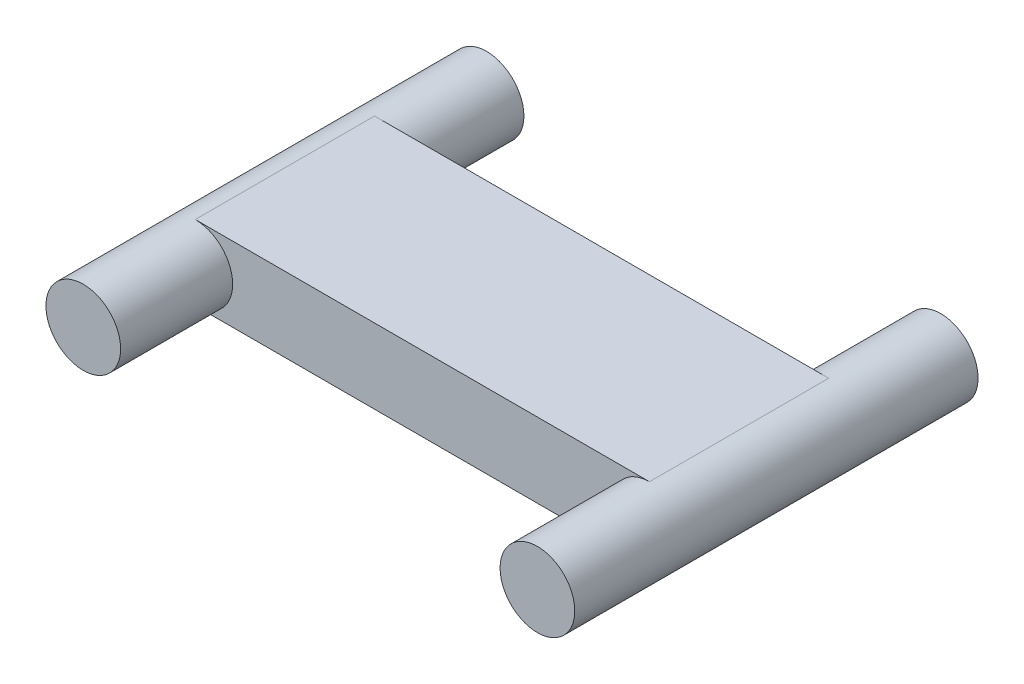
SolidWorks part; units mm, degrees
ref_plane "Front Plane" through (0, 0, 0) normal (0, 0, 1) x (1, 0, 0)
ref_plane "Top Plane" through (0, 0, 0) normal (0, 1, 0) x (1, 0, 0)
ref_plane "Right Plane" through (0, 0, 0) normal (1, 0, 0) x (0, 0, -1)
sketch "Sketch1" plane through (0, 0, 0) normal (0, 0, 1) x (1, 0, 0)
  line L1 (9.6533, 1.5875) -> (-9.6533, 1.5875)
  line L3 (9.6533, -1.5875) -> (-9.6533, -1.5875)
  line L5 (9.6533, 1.5875) -> (-9.6533, -1.5875) construction
  line L6 (9.6533, -1.5875) -> (-9.6533, 1.5875) construction
  arc A0 (-9.6533, 1.5875) -> (-9.6533, -1.5875) centre (-9.6533, 0) ccw
  arc A1 (9.6533, -1.5875) -> (9.6533, 1.5875) centre (9.6533, 0) ccw
  point P0 (0, 0)
  dimension "D1" = 3.175
  dimension "D2" = 19.3065
extrude "Boss-Extrude1" add sketch "Sketch1" along normal mid plane 7.62
sketch "Sketch2" plane through (0, 0, 3.81) normal (0, 0, 1) x (1, 0, 0)
  circle A0 centre (-9.6533, 0) radius 1.5875
  arc A1 (-9.6533, 1.5875) -> (-9.6533, -1.5875) centre (-9.6533, 0) ccw construction
extrude "Boss-Extrude2" add sketch "Sketch2" along normal blind 4.7625
mirror "Mirror1" about plane through (0, 0, 0) normal (1, 0, 0) of "Boss-Extrude2"
mirror "Mirror2" about plane through (0, 0, 0) normal (0, 0, 1) of "Mirror1", "Boss-Extrude2"
